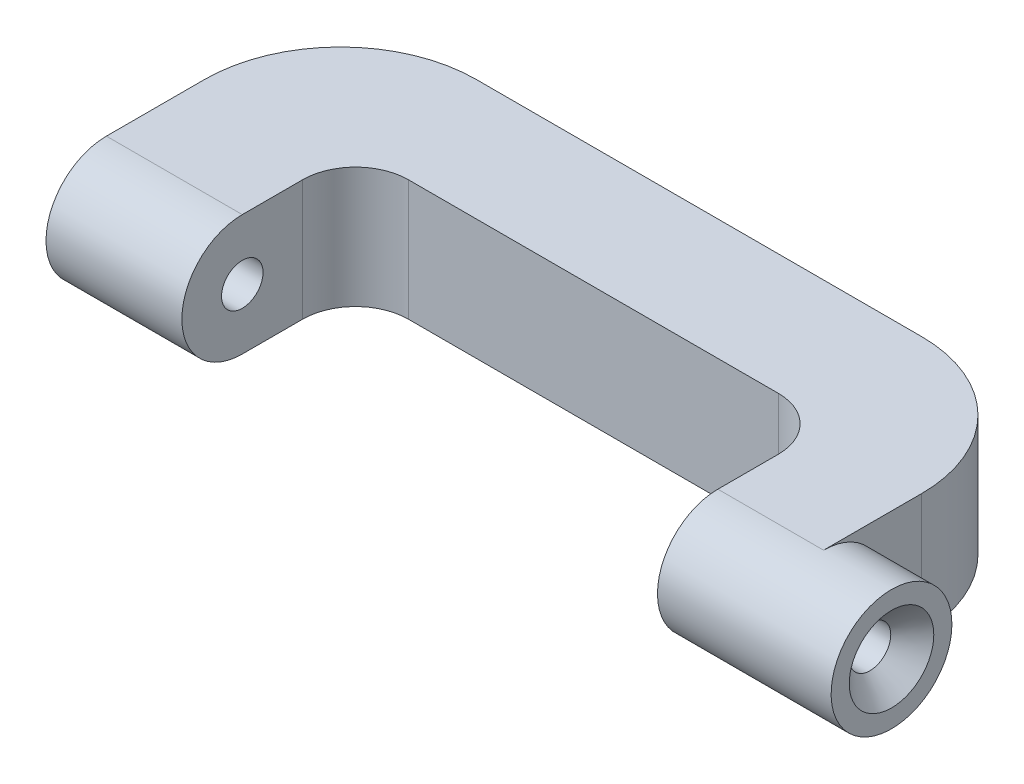
SolidWorks part; units mm, degrees
material "1060 Alloy"
ref_plane "Front Plane" through (0, 0, 0) normal (1, 0, 0) x (0, 1, 0)
ref_plane "Top Plane" through (0, 0, 0) normal (0, 0, 1) x (0, 1, 0)
ref_plane "Right Plane" through (0, 0, 0) normal (0, 1, 0) x (-1, 0, 0)
sketch "Sketch1" plane through (0, 0, 0) normal (1, 0, 0) x (0, 1, 0)
  circle A0 centre (0, 0) radius 8
  dimension "D1" = 16
extrude "Boss-Extrude1" add sketch "Sketch1" along normal blind 18
ref_plane "Plane1" through (81, 0, 0) normal (1, 0, 0) x (0, 0, -1)
sketch "Sketch3" plane through (81, 0, 0) normal (1, 0, 0) x (0, 0, -1)
  circle A0 centre (0, 0) radius 8
  circle A1 centre (0, 0) radius 8 construction
extrude "Boss-Extrude2" add sketch "Sketch3" along normal blind 23 separate body
sketch "Sketch7" plane through (0, 0, 0) normal (0, 1, 0) x (-1, 0, 0)
  line L0 (0, 0) -> (-116.1433, 0) construction
  line L1 (0, 0) -> (0, -13)
  line L2 (-18, -31) -> (-77, -31)
  line L3 (-95, -13) -> (-95, 0)
  line L4 (-95, 0) -> (-81, 0)
  line L5 (-81, 0) -> (-81, -8)
  line L6 (-74, -15) -> (-25, -15)
  line L7 (-18, 8) -> (-18, -8) construction
  line L8 (-18, -8) -> (-18, 0)
  line L9 (-18, 0) -> (0, 0)
  arc A0 (-81, -8) -> (-74, -15) centre (-74, -8) ccw
  arc A1 (-25, -15) -> (-18, -8) centre (-25, -8) ccw
  arc A2 (0, -13) -> (-18, -31) centre (-18, -13) cw
  arc A3 (-77, -31) -> (-95, -13) centre (-77, -13) cw
  point P13 (-81, -15)
  point P17 (-18, -15)
  point P20 (0, -31)
  point P23 (-95, -31)
  dimension "D5" = 7
  dimension "D6" = 18
  dimension "D1" = 31
  dimension "D2" = 95
  dimension "D3" = 14
  dimension "D4" = 15
extrude "Boss-Extrude3" add sketch "Sketch7" along normal mid plane 16
sketch "Sketch5" plane through (104, 0, 0) normal (1, 0, 0) x (0, 1, 0)
  line L0 (0, 0) -> (0, -8) construction
  circle A0 centre (0, 0) radius 8 construction
  point P0 (0, 0)
hole_wizard "CSK for M5 Flat Head Machine Screw1" positions "Sketch5" profile "Sketch6" countersink size "M5" standard "ANSI Metric" end condition through all
sketch "Sketch6" plane through (104, 0, 0) normal (0, 1, 0) x (0, 0, -1)
  line L0 (0, 0) -> (0, 104)
  line L1 (0, 104) -> (2.75, 104)
  line L2 (2.75, 104) -> (2.75, 2.85)
  line L3 (2.75, 2.85) -> (5.6, 0)
  line L5 (5.6, 0) -> (0, 0)
  line L6 (-2.75, 2.85) -> (-5.6, 0) construction
  line L11 (0, -6.35) -> (0, 107.95) construction
  dimension "Thru Hole Dia." = 5.5
  dimension "Thru Hole Depth" = 104
  dimension "Near C'Sink Dia." = 11.2
  dimension "Near C'Sink Angle" = 90
